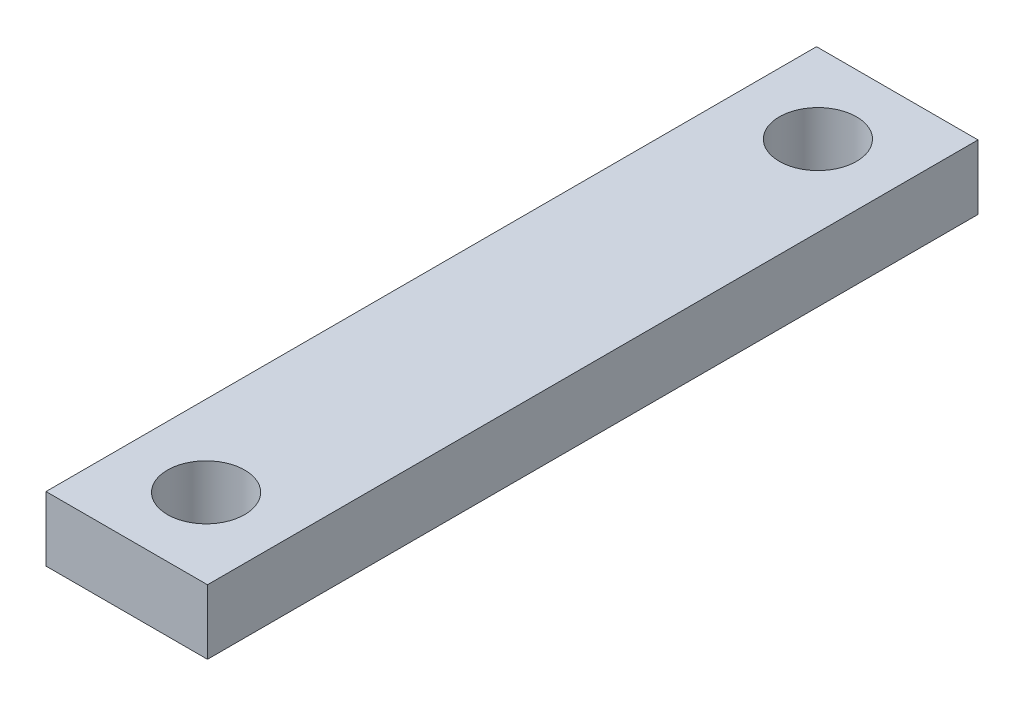
SolidWorks part; units mm, degrees
ref_plane "Front Plane" through (0, 0, 0) normal (0, 0, 1) x (1, 0, 0)
ref_plane "Top Plane" through (0, 0, 0) normal (0, 1, 0) x (1, 0, 0)
ref_plane "Right Plane" through (0, 0, 0) normal (1, 0, 0) x (0, 0, -1)
sketch "Sketch1" plane through (0, 0, 0) normal (0, 0, 1) x (1, 0, 0)
  line L1 (0, 0) -> (7.9375, 0)
  line L2 (0, 0) -> (0, 3.175)
  line L3 (0, 3.175) -> (7.9375, 3.175)
  line L4 (7.9375, 0) -> (7.9375, 3.175)
  dimension "D1" = 7.9375
  dimension "D2" = 3.175
extrude "Boss-Extrude2" add sketch "Sketch1" along normal blind 37.875
sketch "Sketch3" plane through (0, 3.175, 0) normal (0, 1, 0) x (1, 0, 0)
  line L0 (3.9688, 0) -> (3.9688, -37.875) construction
  line L1 (7.9375, 0) -> (0, 0) construction
  line L2 (7.9375, -37.875) -> (0, -37.875) construction
  line L3 (0, -18.9375) -> (7.9375, -18.9375) construction
  line L4 (0, -37.875) -> (0, 0) construction
  line L5 (7.9375, -37.875) -> (7.9375, 0) construction
  circle A0 centre (3.9688, -3.9) radius 1.8987
  circle A1 centre (3.9688, -33.975) radius 1.8987
  dimension "D1" = 3.7973
  dimension "D2" = 3.7973
  dimension "D3" = 15.0375
  dimension "D4" = 15.0375
extrude "Cut-Extrude1" cut sketch "Sketch3" against normal through all
